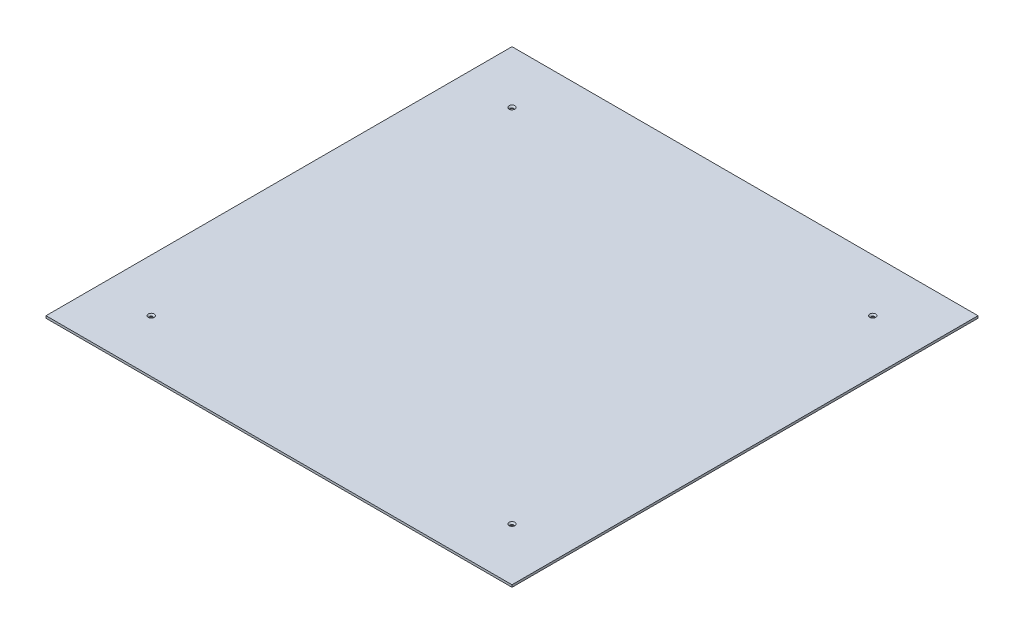
SolidWorks part; units mm, degrees
ref_plane "前视基准面" through (0, 0, 0) normal (0, 0, 1) x (1, 0, 0)
ref_plane "上视基准面" through (0, 0, 0) normal (0, 1, 0) x (1, 0, 0)
ref_plane "右视基准面" through (0, 0, 0) normal (1, 0, 0) x (0, 0, -1)
sketch "草图1" plane through (0, 0, 0) normal (0, 1, 0) x (1, 0, 0)
  line L1 (-155, 155) -> (155, 155)
  line L2 (-155, 155) -> (-155, -155)
  line L3 (-155, -155) -> (155, -155)
  line L4 (155, 155) -> (155, -155)
  line L5 (-155, 155) -> (155, -155) construction
  line L6 (-155, -155) -> (155, 155) construction
  point P0 (0, 0)
  dimension "D1" = 310
  dimension "D2" = 310
extrude "凸台-拉伸1" add sketch "草图1" along normal blind 1.5
hole_wizard "打孔尺寸(%根据)内六角花形沉头螺钉的类型1" positions "草图2" profile "草图3" countersink size "M6" standard "GB" end condition through all
sketch "草图2" plane through (0, 1.5, 0) normal (0, 1, 0) x (1, 0, 0)
  line L0 (155, 155) -> (-155, 155) construction
  line L1 (-155, 155) -> (-155, -155) construction
  point P2 (-120, 120)
  point P19 (120, 120)
  point P20 (120, -120)
  point P21 (-120, -120)
  dimension "D1" = 35
  dimension "D2" = 35
  dimension "D3" = 2
  dimension "D4" = 2
sketch "草图3" plane through (-120, 1.5, -120) normal (1, 0, 0) x (0, 0, 1)
  line L0 (0, 0) -> (0, 1.5)
  line L1 (0, 1.5) -> (1.05, 1.5)
  line L2 (1.05, 1.5) -> (1.05, 0.95)
  line L3 (1.05, 0.95) -> (2, 0)
  line L5 (2, 0) -> (0, 0)
  line L6 (-1.05, 0.95) -> (-2, 0) construction
  line L11 (0, -6.35) -> (0, 107.95) construction
  dimension "通孔孔直径" = 2.1
  dimension "通孔孔深度" = 1.5
  dimension "近端锥形沉头孔直径" = 4
  dimension "近端锥形沉头孔角度" = 90
